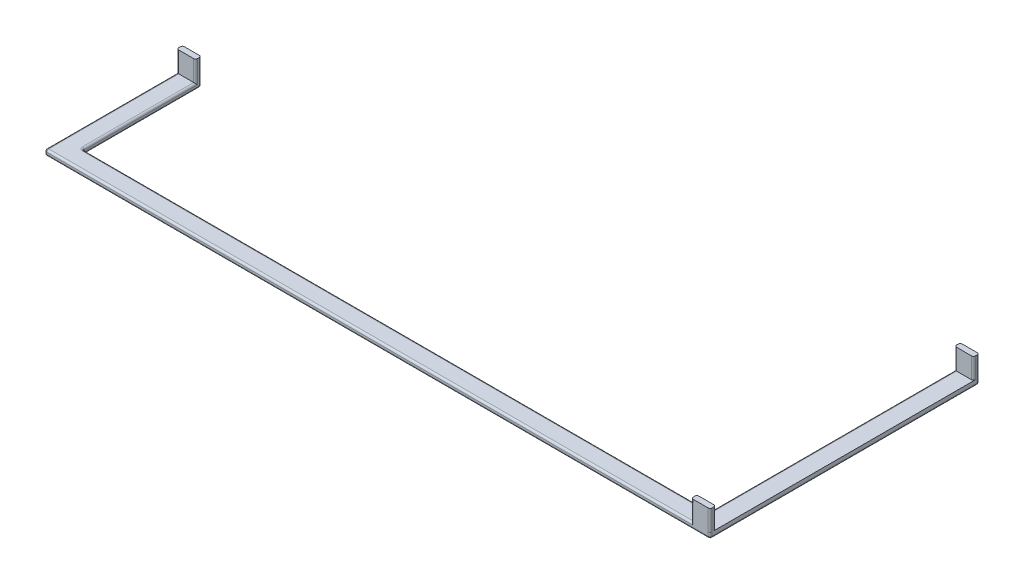
SolidWorks part; units mm, degrees
other "Marquage1"
sketch "Esquisse6" plane through (-343.6, 11, -71.5) normal (-0.0234, 0.4652, -0.8849) x (-0.9769, 0.1773, 0.119)
ref_plane "Plan de face" through (0, 0, 0) normal (0, 0, 1) x (1, 0, 0)
ref_plane "Plan de dessus" through (0, 0, 0) normal (0, 1, 0) x (1, 0, 0)
ref_plane "Plan de droite" through (0, 0, 0) normal (1, 0, 0) x (0, 0, -1)
sketch "Esquisse1" plane through (0, 0, 0) normal (0, 1, 0) x (1, 0, 0)
  line L9 (1, 71.5) -> (9, 71.5)
  line L10 (0, 70.5) -> (0, 69.5)
  line L11 (1, 68.5) -> (9, 68.5)
  line L12 (10, 70.5) -> (10, 69.5)
  line L13 (1, -68.5) -> (9, -68.5)
  line L14 (0, -69.5) -> (0, -70.5)
  line L15 (1, -71.5) -> (9, -71.5)
  line L16 (10, -69.5) -> (10, -70.5)
  arc A8 (9, 68.5) -> (10, 69.5) centre (9, 69.5) ccw
  arc A9 (9, 71.5) -> (10, 70.5) centre (9, 70.5) cw
  arc A10 (1, 71.5) -> (0, 70.5) centre (1, 70.5) ccw
  arc A11 (0, 69.5) -> (1, 68.5) centre (1, 69.5) ccw
  arc A12 (9, -68.5) -> (10, -69.5) centre (9, -69.5) cw
  arc A13 (9, -71.5) -> (10, -70.5) centre (9, -70.5) ccw
  arc A14 (1, -68.5) -> (0, -69.5) centre (1, -69.5) ccw
  arc A15 (0, -70.5) -> (1, -71.5) centre (1, -70.5) ccw
  point P43 (0, -70)
  point P45 (0, 70)
  point P61 (10, -71.5)
  point P66 (0, -71.5)
  dimension "D9" = 1
  dimension "D10" = 1
  dimension "D2" = 70
  dimension "D3" = 70
  dimension "D7" = 3
  dimension "D8" = 3
  dimension "D12" = 10
extrude "Boss.-Extru.1" add sketch "Esquisse1" along normal blind 11
sketch "Esquisse2" plane through (0, 0, 0) normal (0, -1, 0) x (1, 0, 0)
  line L0 (10, -69.5) -> (10, -70.5) construction
  line L1 (0, 71.5) -> (10, 71.5)
  line L2 (0, 71.5) -> (0, -71.5)
  line L3 (0, -71.5) -> (10, -71.5)
  line L4 (10, 71.5) -> (10, -71.5)
  line L5 (9, -71.5) -> (1, -71.5) construction
  line L6 (0, -70.5) -> (0, -69.5) construction
  line L7 (1, 71.5) -> (9, 71.5) construction
extrude "Boss.-Extru.2" add sketch "Esquisse2" along normal blind 3
sketch "Esquisse3" plane through (0, 0, 0) normal (1, 0, 0) x (0, 0, -1)
  line L0 (69.5, 0) -> (-69.5, 0) construction
  line L1 (-61.5, -3) -> (-71.5, -3)
  line L2 (-61.5, -3) -> (-61.5, 0)
  line L3 (-61.5, 0) -> (-71.5, 0)
  line L4 (-71.5, -3) -> (-71.5, 0)
  line L5 (-71.5, -3) -> (-71.5, 0) construction
  line L6 (-71.5, -3) -> (71.5, -3) construction
  dimension "D1" = 10
extrude "Boss.-Extru.4" add sketch "Esquisse3" against normal blind 343.6
sketch "Esquisse4" plane through (0, 0, 61.5) normal (0, 0, -1) x (-1, 0, 0)
  line L0 (343.6, 0) -> (0, 0) construction
  line L1 (343.6, -3) -> (333.6, -3)
  line L2 (343.6, -3) -> (343.6, 0)
  line L3 (343.6, 0) -> (333.6, 0)
  line L4 (333.6, -3) -> (333.6, 0)
  dimension "D1" = 10
extrude "Boss.-Extru.5" add sketch "Esquisse4" along normal blind 63.11
sketch "Esquisse5" plane through (0, 0, 0) normal (0, 1, 0) x (1, 0, 0)
  line L7 (-342.6, 1.61) -> (-334.6, 1.61)
  line L8 (-343.6, 0.61) -> (-343.6, -0.39)
  line L9 (-342.6, -1.39) -> (-334.6, -1.39)
  line L10 (-333.6, 0.61) -> (-333.6, -0.39)
  line L11 (-343.6, 1.61) -> (-343.6, -71.5) construction
  line L12 (-343.6, 1.61) -> (-333.6, 1.61) construction
  line L13 (-333.6, 1.61) -> (-333.6, -61.5) construction
  arc A2 (-333.6, -0.39) -> (-334.6, -1.39) centre (-334.6, -0.39) cw
  arc A3 (-333.6, 0.61) -> (-334.6, 1.61) centre (-334.6, 0.61) ccw
  arc A4 (-343.6, 0.61) -> (-342.6, 1.61) centre (-342.6, 0.61) cw
  arc A5 (-343.6, -0.39) -> (-342.6, -1.39) centre (-342.6, -0.39) ccw
  dimension "D1" = 1
  dimension "D2" = 3
extrude "Boss.-Extru.6" add sketch "Esquisse5" along normal up to surface (11 mm away) up to face at (5, 11, -70)
fillet "Congé1" radius 1 8 edges at (-333.6, -1.5, -1.61) (-343.6, -1.5, -1.61) (-343.6, -1.5, 71.5) (-333.6, -1.5, 61.5) (0, -1.5, 61.5) (0, -1.5, -71.5) (10, -1.5, -71.5) (10, -1.5, 71.5)
ref_plane "Plan1" through (-166.8, 0, 0) normal (-1, 0, 0) x (0, 0, 1)
fillet "Congé2" radius 1 24 edges at (-166.8, -3, 61.5) (-333.3071, 0, 61.2071) (-333.3071, -3, 61.2071) (-333.6, -3, 29.945) (-333.8929, -3, -1.3171) (-338.6, -3, -1.61) (-343.3071, -3, -1.3171) (-343.6, -3, 34.945) (-343.3071, 0, 71.2071) (-343.3071, -3, 71.2071) (-333.6, 0, 30.445) (-343.6, 0, 35.445) (-170.8, 0, 71.5) (-166.8, -3, 71.5) (-166.8, 0, 61.5) (9.7071, -3, 71.2071) (10, -3, 0) (9.7071, -3, -71.2071) (5, -3, -71.5) (0.2929, -3, -71.2071) (0, -3, -5) (-0.2929, -3, 61.2071) (-0.2929, 0, 61.2071) (0, 0, -4.5)
